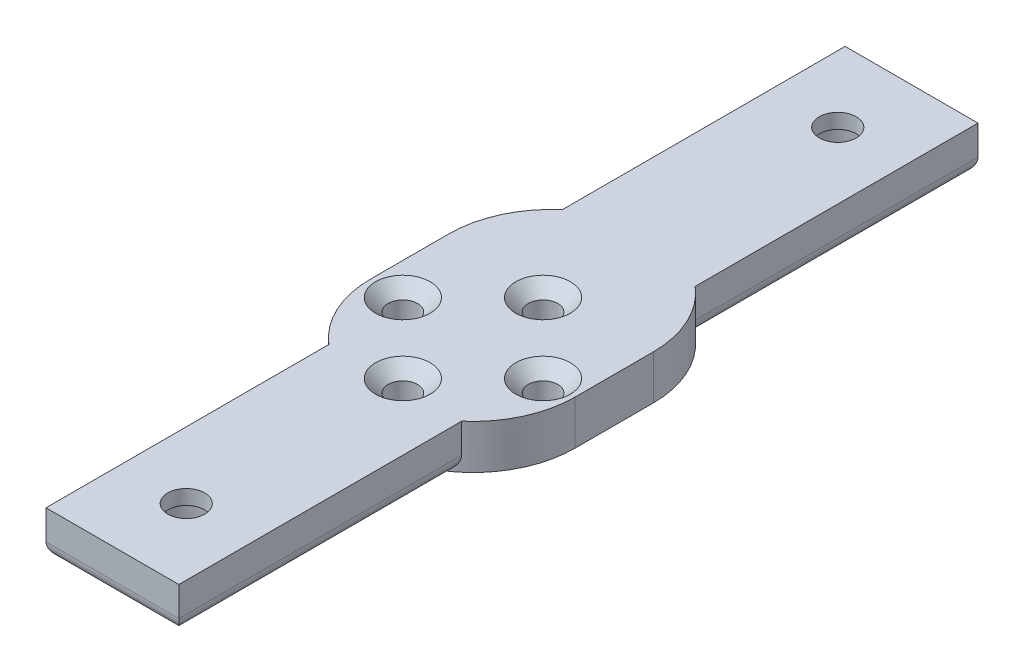
SolidWorks part; units mm, degrees
ref_plane "Front Plane" through (0, 0, 0) normal (0, 0, 1) x (1, 0, 0)
ref_plane "Top Plane" through (0, 0, 0) normal (0, 1, 0) x (1, 0, 0)
ref_plane "Right Plane" through (0, 0, 0) normal (1, 0, 0) x (0, 0, -1)
sketch "Sketch1" plane through (0, 0, 0) normal (0, 1, 0) x (1, 0, 0)
  line L0 (-13.85, 0) -> (13.85, 0) construction
  line L10 (-13.85, 5.29) -> (-13.85, -5.29)
  line L12 (13.85, 5.29) -> (13.85, -5.29)
  line L13 (-13.85, 5.29) -> (13.85, -5.29) construction
  line L14 (-13.85, -5.29) -> (13.85, 5.29) construction
  line L15 (9, 15.8172) -> (9, 54.14)
  line L16 (-9, -54.14) -> (9, -54.14)
  line L17 (-9, -54.14) -> (-9, -15.8172)
  line L18 (-9, 54.14) -> (9, 54.14)
  line L19 (9, -54.14) -> (9, -15.8172)
  line L20 (-9, -54.14) -> (9, 54.14) construction
  line L21 (-9, 54.14) -> (9, -54.14) construction
  line L22 (-9, 15.8172) -> (-9, 54.14)
  arc A1 (13.85, 5.29) -> (9, 15.8172) centre (0, 5.29) ccw
  arc A2 (-13.85, -5.29) -> (-9, -15.8172) centre (0, -5.29) ccw
  arc A3 (9, -15.8172) -> (13.85, -5.29) centre (0, -5.29) ccw
  arc A4 (-9, 15.8172) -> (-13.85, 5.29) centre (0, 5.29) ccw
  point P0 (0, 0)
  point P10 (0, 0)
  dimension "D2" = 10.58
  dimension "D5" = 18
  dimension "D1" = 27.7
  dimension "D3" = 13.85
  dimension "D4" = 13.85
  dimension "D6" = 108.28
extrude "Boss-Extrude1" add sketch "Sketch1" along normal blind 6
sketch "Sketch4" plane through (0, 6, 0) normal (0, 1, 0) x (1, 0, 0)
  line L0 (9, 54.14) -> (-9, 54.14) construction
  line L1 (-9, -54.14) -> (9, -54.14) construction
  line L2 (-13.85, -5.29) -> (13.85, -5.29) construction
  circle A0 centre (0, 44.14) radius 2.5
  circle A1 centre (0, -44.14) radius 2.5
  circle A2 centre (-9.5, -5.29) radius 2
  circle A3 centre (9.5, -5.29) radius 2
  circle A4 centre (0, 4.21) radius 2
  circle A5 centre (0, -14.79) radius 2
  dimension "D1" = 5
  dimension "D3" = 5
  dimension "D4" = 10
  dimension "D5" = 4
  dimension "D6" = 4
  dimension "D9" = 4
  dimension "D11" = 4
  dimension "D2" = 10
  dimension "D7" = 4.35
  dimension "D8" = 4.35
  dimension "D10" = 9.5
  dimension "D12" = 9.5
extrude "Cut-Extrude1" cut sketch "Sketch4" against normal blind 6
chamfer "Chamfer1" distance 1.7 4 edges at (9.5, 6, 7.29) (0, 6, 16.79) (-9.5, 6, 7.29) (0, 6, -2.21)
fillet "Fillet1" radius 2 6 edges at (9, 0, -34.9786) (0, 0, -54.14) (-9, 0, -34.9786) (-9, 0, 34.9786) (0, 0, 54.14) (9, 0, 34.9786)
sketch "Sketch5" plane through (0, 0, 0) normal (0, -1, 0) x (1, 0, 0)
  circle A0 centre (0, -44.14) radius 4.25
  circle A1 centre (0, 44.14) radius 4.25
  dimension "D1" = 8.5
extrude "Cut-Extrude2" cut sketch "Sketch5" against normal blind 4
